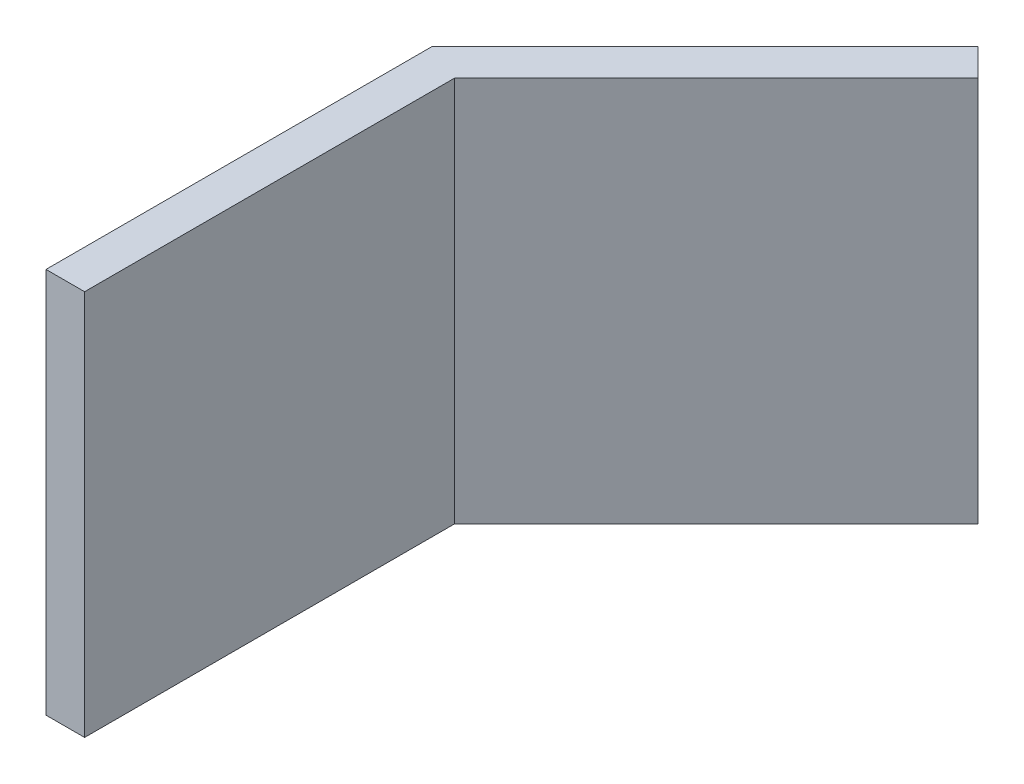
SolidWorks part; units mm, degrees
ref_plane "Plan de face" through (0, 0, 0) normal (0, 0, 1) x (1, 0, 0)
ref_plane "Plan de dessus" through (0, 0, 0) normal (0, 1, 0) x (1, 0, 0)
ref_plane "Plan de droite" through (0, 0, 0) normal (1, 0, 0) x (0, 0, -1)
sketch "Esquisse1" plane through (0, 0, 0) normal (0, 1, 0) x (1, 0, 0)
  line L0 (0, 0) -> (0, 20)
  line L1 (0, 20) -> (14.1421, 34.1421)
  line L2 (14.1421, 34.1421) -> (15.5563, 32.7279)
  line L3 (15.5563, 32.7279) -> (2, 19.1716)
  line L4 (2, 19.1716) -> (2, 0)
  line L5 (2, 0) -> (0, 0)
  dimension "D1" = 2
  dimension "D2" = 20
  dimension "D3" = 45
extrude "Extrusion1" add sketch "Esquisse1" along normal blind 20
